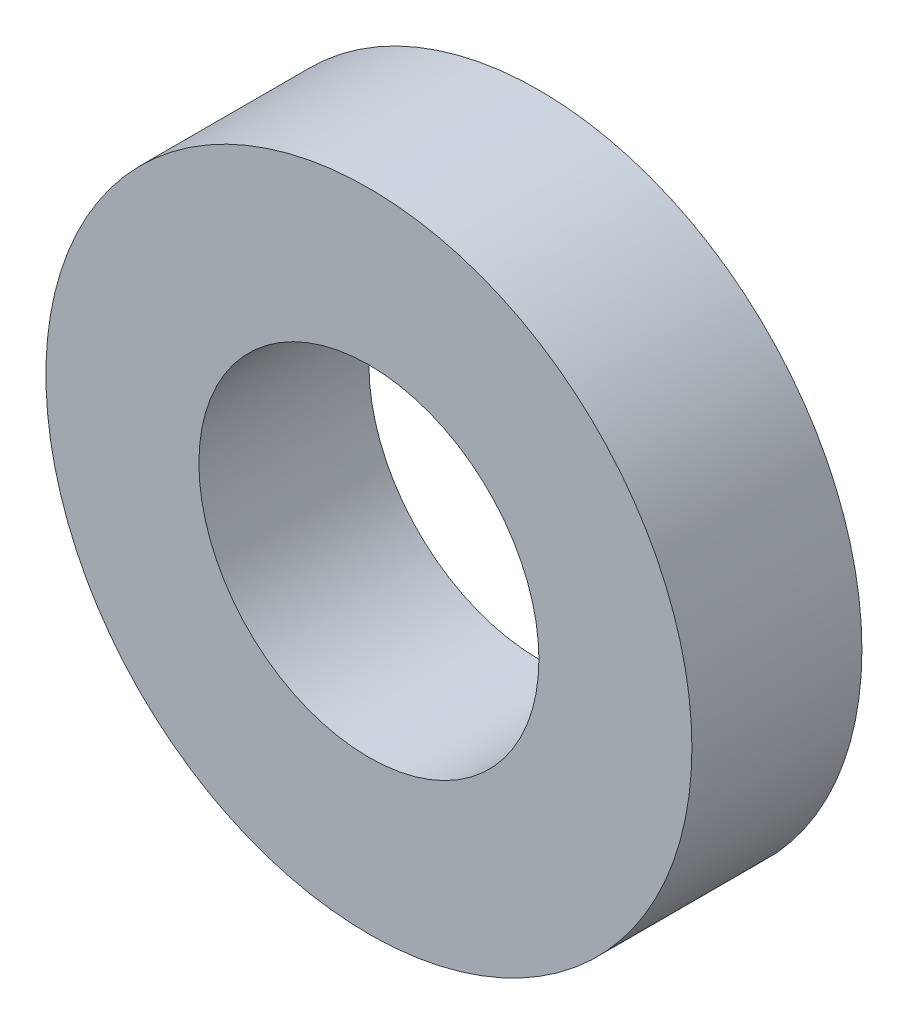
SolidWorks part; units mm, degrees
material "AISI 304"
ref_plane "정면" through (0, 0, 0) normal (0, 0, 1) x (1, 0, 0)
ref_plane "윗면" through (0, 0, 0) normal (0, 1, 0) x (1, 0, 0)
ref_plane "우측면" through (0, 0, 0) normal (1, 0, 0) x (0, 0, -1)
sketch "스케치1" plane through (0, 0, 0) normal (0, 0, 1) x (1, 0, 0)
  circle A0 centre (0, 0) radius 5
  circle A1 centre (0, 0) radius 9.5
  dimension "D1" = 19
  dimension "D2" = 10
extrude "보스-돌출1" add sketch "스케치1" along normal blind 5
